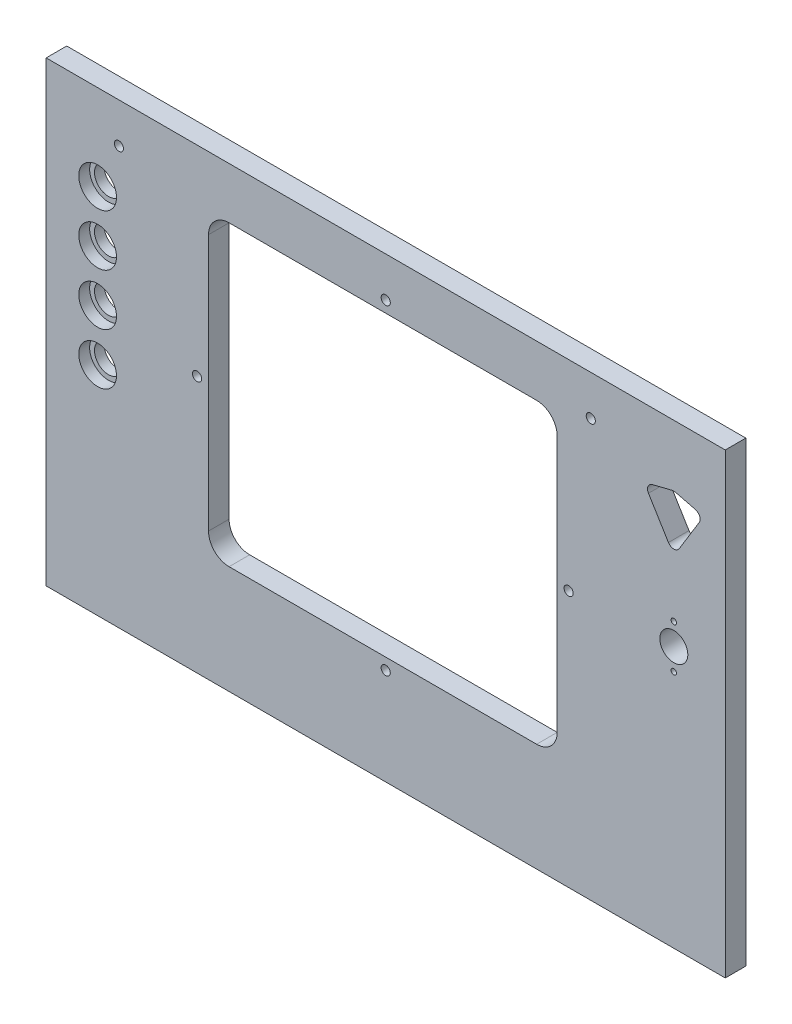
SolidWorks part; units mm, degrees
ref_plane "Front Plane" through (0, 0, 0) normal (0, 0, 1) x (1, 0, 0)
ref_plane "Top Plane" through (0, 0, 0) normal (0, 1, 0) x (1, 0, 0)
ref_plane "Right Plane" through (0, 0, 0) normal (1, 0, 0) x (0, 0, -1)
sketch "Sketch1" plane through (0, 0, 0) normal (0, 0, 1) x (1, 0, 0)
  line L1 (-297, -200) -> (297, -200)
  line L2 (-297, -200) -> (-297, 200)
  line L3 (-297, 200) -> (297, 200)
  line L4 (297, -200) -> (297, 200)
  line L5 (-297, -200) -> (297, 200) construction
  line L6 (-297, 200) -> (297, -200) construction
  line L7 (-137, -105.42) -> (132, -105.42)
  line L8 (-155, -87.42) -> (-155, 137.08)
  line L9 (-137, 155.08) -> (132, 155.08)
  line L10 (150, -87.42) -> (150, 137.08)
  line L11 (-155, -105.42) -> (150, 155.08) construction
  line L12 (-155, 155.08) -> (150, -105.42) construction
  line L20 (254.386, 145.9793) -> (270.8081, 141.8458)
  line L21 (274.1662, 133.6255) -> (256.7037, 105.0505)
  line L22 (247.2963, 105.0505) -> (229.8338, 133.6255)
  line L23 (233.1919, 141.8458) -> (249.614, 145.9793)
  circle A4 centre (252, 28.55) radius 12.25
  circle A5 centre (-252, 125) radius 12.25
  circle A6 centre (-252, 80) radius 12.25
  circle A7 centre (-252, 35) radius 12.25
  circle A8 centre (-252, -10) radius 12.25
  arc A9 (-137, -105.42) -> (-155, -87.42) centre (-137, -87.42) cw
  arc A10 (132, -105.42) -> (150, -87.42) centre (132, -87.42) ccw
  arc A11 (132, 155.08) -> (150, 137.08) centre (132, 137.08) cw
  arc A12 (-155, 137.08) -> (-137, 155.08) centre (-137, 137.08) cw
  arc A17 (274.1662, 133.6255) -> (270.8081, 141.8458) centre (269.4625, 136.5) ccw
  arc A18 (247.2963, 105.0505) -> (256.7037, 105.0505) centre (252, 107.925) ccw
  arc A19 (233.1919, 141.8458) -> (229.8338, 133.6255) centre (234.5375, 136.5) ccw
  arc A20 (254.386, 145.9793) -> (249.614, 145.9793) centre (252, 136.5) ccw
  point P0 (0, 0)
  point P6 (0, 0)
  dimension "D11" = 24.5
  dimension "D12" = 24.5
  dimension "D14" = 45
  dimension "D15" = 44.92
  dimension "D16" = 45
  dimension "D17" = 24.5
  dimension "D23" = 45
  dimension "D24" = 45
  dimension "D25" = 45
  dimension "D26" = 24.5
  dimension "D27" = 18
  dimension "D28" = 142
  dimension "D1" = 594
  dimension "D2" = 400
  dimension "D18" = 260.5
  dimension "D19" = 305
  dimension "D13" = 2
extrude "Boss-Extrude1" add sketch "Sketch1" along normal blind 18
sketch "Sketch2" plane through (0, 0, 18) normal (0, 0, 1) x (1, 0, 0)
  circle A0 centre (-252, 125) radius 16.5
  circle A1 centre (-252, 80) radius 16.5
  circle A2 centre (-252, 35) radius 16.5
  circle A5 centre (-252, -10) radius 16.5
  dimension "D1" = 33
  dimension "D2" = 33
  dimension "D3" = 33
  dimension "D5" = 33
extrude "Cut-Extrude1" cut sketch "Sketch2" against normal blind 9.525
sketch "Sketch3" plane through (0, 0, 18) normal (0, 0, 1) x (1, 0, 0)
  line L0 (297, 200) -> (-297, 200) construction
  line L1 (-155, 137.08) -> (-155, -87.42) construction
  line L2 (150, -87.42) -> (150, 137.08) construction
  line L3 (-137, -105.42) -> (132, -105.42) construction
  line L4 (-297, 200) -> (-297, -200) construction
  line L5 (297, -200) -> (297, 200) construction
  circle A0 centre (0, 165.075) radius 4
  circle A1 centre (-233.3625, 165.075) radius 4
  circle A2 centre (179.3875, 165.075) radius 4
  circle A3 centre (0, -115.42) radius 4
  circle A4 centre (-165, 24.83) radius 4
  circle A5 centre (160, 24.83) radius 4
  dimension "D1" = 8
  dimension "D2" = 8
  dimension "D3" = 8
  dimension "D4" = 233.3625
  dimension "D5" = 179.3875
  dimension "D7" = 34.925
  dimension "D9" = 34.925
  dimension "D10" = 8
  dimension "D11" = 8
  dimension "D12" = 8
  dimension "D13" = 10
  dimension "D14" = 10
  dimension "D19" = 160
  dimension "D6" = 0
  dimension "D8" = 34.925
  dimension "D15" = 10
  dimension "D16" = 297
  dimension "D17" = 297
  dimension "D18" = 155
extrude "Cut-Extrude2" cut sketch "Sketch3" against normal blind 80
sketch "Sketch4" plane through (0, 0, 18) normal (0, 0, 1) x (1, 0, 0)
  circle A0 centre (252, 47.6) radius 2.3813
  circle A1 centre (252, 9.5) radius 2.3813
  circle A2 centre (252, 28.55) radius 12.25 construction
  dimension "D1" = 38.1
  dimension "D2" = 19.05
  dimension "D3" = 4.7625
  dimension "D4" = 4.7625
extrude "Cut-Extrude3" cut sketch "Sketch4" against normal blind 9.525
